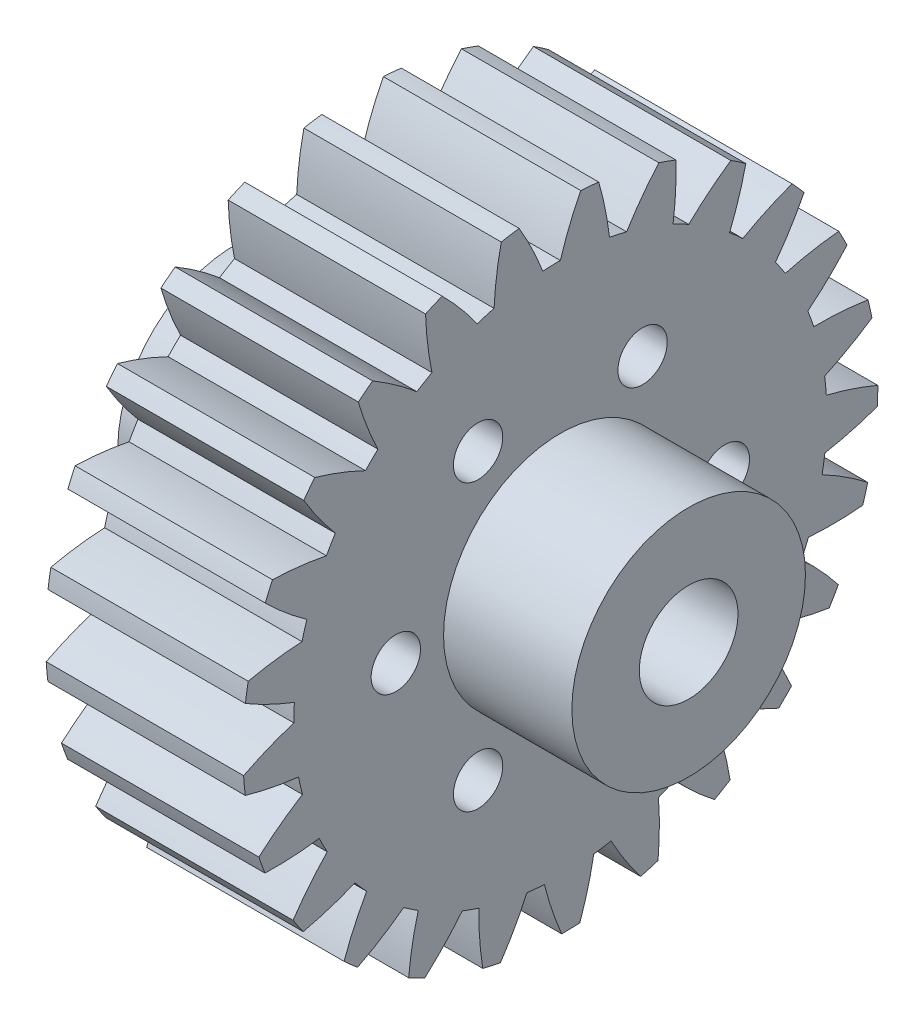
SolidWorks part; units mm, degrees
ref_plane "Front Plane" through (0, 0, 0) normal (0, 0, 1) x (1, 0, 0)
ref_plane "Top Plane" through (0, 0, 0) normal (0, 1, 0) x (1, 0, 0)
ref_plane "Right Plane" through (0, 0, 0) normal (1, 0, 0) x (0, 0, -1)
sketch "Sketch1" plane through (0, 0, 0) normal (1, 0, 0) x (0, 0, -1)
  line L0 (0, 0) -> (1.787, 19.2171) construction
  circle A1 centre (0, 0) radius 19.3 construction
  circle A3 centre (0, 0) radius 3
  arc A5 (1.2387, 19.2602) -> (2.3339, 19.1584) centre (0, 0) cw
  circle A6 centre (0, 0) radius 17.9 construction
  arc A105 (2.7, 17.6952) -> (0.6091, 17.8896) centre (0, 0) ccw
  arc A107 (0, 16.2) -> (1.2387, 19.2602) centre (18.6515, 10.4313) cw
  arc A109 (2.3339, 19.1584) -> (2.9871, 15.9222) centre (-16.4082, 13.6916) cw
  arc A111 (15.4071, 5.0061) -> (15.0442, 6.0095) centre (0, 0) ccw
  arc A113 (7.0251, 17.976) -> (6.853, 14.6791) centre (-12.4878, 17.342) cw
  arc A115 (5.9896, 18.3471) -> (7.0251, 17.976) centre (0, 0) cw
  arc A117 (4.0288, 15.691) -> (5.9896, 18.3471) centre (20.6596, 5.4651) cw
  arc A118 (11.2749, 15.6642) -> (10.2882, 12.5137) centre (-7.7827, 19.9027) cw
  arc A120 (10.3641, 16.2811) -> (11.2749, 15.6642) centre (0, 0) cw
  arc A122 (7.8044, 14.1962) -> (10.3641, 16.2811) centre (21.3697, 0.1556) cw
  arc A124 (14.8162, 12.3681) -> (13.077, 9.562) centre (-2.5886, 21.2129) cw
  arc A126 (14.0875, 13.1922) -> (14.8162, 12.3681) centre (0, 0) cw
  arc A128 (11.0897, 11.8093) -> (14.0875, 13.1922) centre (20.737, -5.1637) cw
  arc A131 (17.4265, 8.2949) -> (15.0442, 6.0095) centre (2.7682, 21.1902) cw
  arc A132 (16.9256, 9.2743) -> (17.4265, 8.2949) centre (0, 0) cw
  arc A134 (13.6781, 8.6804) -> (16.9256, 9.2743) centre (18.8014, -10.1586) cw
  arc A136 (18.9419, 3.7005) -> (16.066, 2.0793) centre (7.951, 19.8361) cw
  arc A138 (18.7003, 4.7737) -> (18.9419, 3.7005) centre (0, 0) cw
  arc A140 (15.4071, 5.0061) -> (18.7003, 4.7737) centre (15.6844, -14.5151) cw
  arc A143 (19.2671, -1.1264) -> (16.0784, -1.9815) centre (12.6343, 17.2355) cw
  arc A145 (19.3, -0.0269) -> (19.2671, -1.1264) centre (0, 0) cw
  arc A146 (16.168, 1.0172) -> (19.3, -0.0269) centre (11.5818, -17.9597) cw
  arc A148 (18.3817, -5.8825) -> (15.0805, -5.9177) centre (16.5236, 13.5521) cw
  arc A150 (18.687, -4.8257) -> (18.3817, -5.8825) centre (0, 0) cw
  arc A153 (15.9131, -3.0356) -> (18.687, -4.8257) centre (6.7516, -20.2757) cw
  arc A154 (16.3413, -10.2691) -> (13.135, -9.4822) centre (19.3748, 9.017) cw
  arc A155 (16.8998, -9.3214) -> (16.3413, -10.2691) centre (0, 0) cw
  arc A156 (14.6582, -6.8976) -> (16.8998, -9.3214) centre (1.4971, -21.3178) cw
  arc A157 (13.2741, -14.0103) -> (10.3642, -12.4508) centre (21.0085, 3.9154) cw
  arc A158 (14.0507, -13.2313) -> (13.2741, -14.0103) centre (0, 0) cw
  arc A159 (12.4823, -10.3263) -> (14.0507, -13.2313) centre (-3.8514, -21.0203) cw
  arc A160 (9.3728, -16.8713) -> (6.9422, -14.6371) centre (21.3222, -1.4322) cw
  arc A161 (10.3188, -16.3099) -> (9.3728, -16.8713) centre (0, 0) cw
  arc A162 (9.5221, -13.1061) -> (10.3188, -16.3099) centre (-8.958, -19.4021) cw
  arc A163 (4.8826, -18.6722) -> (3.084, -15.9037) centre (20.2962, -6.6898) cw
  arc A164 (5.9385, -18.3637) -> (4.8826, -18.6722) centre (0, 0) cw
  arc A165 (5.9636, -15.0624) -> (5.9385, -18.3637) centre (-13.5017, -16.5648) cw
  arc A166 (0.0856, -19.2998) -> (-0.968, -16.1711) centre (17.9949, -11.5271) cw
  arc A167 (1.185, -19.2636) -> (0.0856, -19.2998) centre (0, 0) cw
  arc A168 (2.0304, -16.0723) -> (1.185, -19.2636) centre (-17.197, -12.6867) cw
  arc A169 (-4.7167, -18.7148) -> (-4.9591, -15.4223) centre (14.5628, -15.6401) cw
  arc A170 (-3.6429, -18.9531) -> (-4.7167, -18.7148) centre (0, 0) cw
  arc A171 (-2.0304, -16.0723) -> (-3.6429, -18.9531) centre (-19.8118, -8.0114) cw
  arc A172 (-9.2227, -16.9538) -> (-8.6387, -13.7045) centre (10.2158, -18.7704) cw
  arc A173 (-8.2418, -17.4517) -> (-9.2227, -16.9538) centre (0, 0) cw
  arc A174 (-5.9636, -15.0624) -> (-8.2418, -17.4517) centre (-21.1817, -2.8327) cw
  arc A175 (-13.1492, -14.1276) -> (-11.7755, -11.1256) centre (5.2268, -20.7212) cw
  arc A176 (-12.323, -14.8538) -> (-13.1492, -14.1276) centre (0, 0) cw
  arc A177 (-9.5221, -13.1061) -> (-12.323, -14.8538) centre (-21.2207, 2.524) cw
  arc A178 (-16.2495, -10.4137) -> (-14.1723, -7.8476) centre (-0.0905, -21.3701) cw
  arc A179 (-15.6298, -11.3225) -> (-16.2495, -10.4137) centre (0, 0) cw
  arc A180 (-12.4823, -10.3263) -> (-15.6298, -11.3225) centre (-19.9263, 7.722) cw
  arc A181 (-18.3287, -6.0454) -> (-15.6787, -4.0765) centre (-5.4022, -20.6762) cw
  arc A182 (-17.9546, -7.0798) -> (-18.3287, -6.0454) centre (0, 0) cw
  arc A183 (-14.6582, -6.8976) -> (-17.9546, -7.0798) centre (-17.3799, 12.4349) cw
  arc A184 (-19.2563, -1.2973) -> (-16.1999, -0.0493) centre (-10.3744, -18.6831) cw
  arc A185 (-19.1512, -2.3923) -> (-19.2563, -1.2973) centre (0, 0) cw
  arc A186 (-15.9131, -3.0356) -> (-19.1512, -2.3923) centre (-13.7415, 16.3665) cw
  arc A187 (-18.974, 3.5323) -> (-15.7032, 3.981) centre (-14.6948, -15.5161) cw
  arc A188 (-19.1444, 2.4456) -> (-18.974, 3.5323) centre (0, 0) cw
  arc A189 (-16.168, 1.0172) -> (-19.1444, 2.4456) centre (-9.2396, 19.2696) cw
  arc A190 (-17.4995, 8.14) -> (-14.2199, 7.7611) centre (-18.0919, -11.3742) cw
  arc A191 (-17.9348, 7.1298) -> (-17.4995, 8.14) centre (0, 0) cw
  arc A192 (-15.4071, 5.0061) -> (-17.9348, 7.1298) centre (-4.1571, 20.962) cw
  arc A193 (-14.9253, 12.2362) -> (-11.843, 11.0537) centre (-20.3521, -6.5176) cw
  arc A194 (-15.5982, 11.366) -> (-14.9253, 12.2362) centre (0, 0) cw
  arc A195 (-13.6781, 8.6804) -> (-15.5982, 11.366) centre (1.1865, 21.3373) cw
  arc A196 (-11.4134, 15.5635) -> (-8.722, 13.6516) centre (-21.3336, -1.2515) cw
  arc A197 (-12.2816, 14.888) -> (-11.4134, 15.5635) centre (0, 0) cw
  arc A198 (-11.0897, 11.8093) -> (-12.2816, 14.888) centre (6.4556, 20.3719) cw
  arc A199 (-7.1844, 17.913) -> (-5.053, 15.3918) centre (-20.9746, 4.0933) cw
  arc A200 (-8.1932, 17.4746) -> (-7.1844, 17.913) centre (0, 0) cw
  arc A201 (-7.8044, 14.1962) -> (-8.1932, 17.4746) centre (11.3191, 18.1264) cw
  arc A202 (-2.5039, 19.1369) -> (-1.0664, 16.1649) centre (-19.2977, 9.1809) cw
  arc A203 (-3.5901, 18.9632) -> (-2.5039, 19.1369) centre (0, 0) cw
  arc A204 (-4.0288, 15.691) -> (-3.5901, 18.9632) centre (15.4713, 14.742) cw
  arc A205 (13.6781, 8.6804) -> (13.077, 9.562) centre (0, 0) ccw
  arc A206 (11.0897, 11.8093) -> (10.2882, 12.5137) centre (0, 0) ccw
  arc A207 (7.8044, 14.1962) -> (6.853, 14.6791) centre (0, 0) ccw
  arc A208 (4.0288, 15.691) -> (2.9871, 15.9222) centre (0, 0) ccw
  arc A209 (16.168, 1.0172) -> (16.066, 2.0793) centre (0, 0) ccw
  arc A210 (15.9131, -3.0356) -> (16.0784, -1.9815) centre (0, 0) ccw
  arc A211 (14.6582, -6.8976) -> (15.0805, -5.9177) centre (0, 0) ccw
  arc A212 (12.4823, -10.3263) -> (13.135, -9.4822) centre (0, 0) ccw
  arc A213 (9.5221, -13.1061) -> (10.3642, -12.4508) centre (0, 0) ccw
  arc A214 (5.9636, -15.0624) -> (6.9422, -14.6371) centre (0, 0) ccw
  arc A215 (2.0304, -16.0723) -> (3.084, -15.9037) centre (0, 0) ccw
  arc A216 (-2.0304, -16.0723) -> (-0.968, -16.1711) centre (0, 0) ccw
  arc A217 (-5.9636, -15.0624) -> (-4.9591, -15.4223) centre (0, 0) ccw
  arc A218 (-9.5221, -13.1061) -> (-8.6387, -13.7045) centre (0, 0) ccw
  arc A219 (-12.4823, -10.3263) -> (-11.7755, -11.1256) centre (0, 0) ccw
  arc A220 (-14.6582, -6.8976) -> (-14.1723, -7.8476) centre (0, 0) ccw
  arc A221 (-15.9131, -3.0356) -> (-15.6787, -4.0765) centre (0, 0) ccw
  arc A222 (-16.168, 1.0172) -> (-16.1999, -0.0493) centre (0, 0) ccw
  arc A223 (-15.4071, 5.0061) -> (-15.7032, 3.981) centre (0, 0) ccw
  arc A224 (-13.6781, 8.6804) -> (-14.2199, 7.7611) centre (0, 0) ccw
  arc A225 (-4.0288, 15.691) -> (-5.053, 15.3918) centre (0, 0) ccw
  arc A226 (-7.8044, 14.1962) -> (-8.722, 13.6516) centre (0, 0) ccw
  arc A227 (-11.0897, 11.8093) -> (-11.843, 11.0537) centre (0, 0) ccw
  arc A228 (0, 16.2) -> (-1.0664, 16.1649) centre (0, 0) ccw
  circle A229 centre (0, 0) radius 10 construction
  circle A230 centre (10, 0) radius 1.5
  circle A231 centre (5, -8.6603) radius 1.5
  circle A232 centre (-5, -8.6603) radius 1.5
  circle A233 centre (-10, 0) radius 1.5
  circle A234 centre (-5, 8.6603) radius 1.5
  circle A235 centre (5, 8.6603) radius 1.5
  point P10 (1.787, 19.2171)
  point P13 (1.6574, 17.8231)
  point P160 (0, 0)
  point P165 (0, 0)
  point P177 (0, 0)
  dimension "D1" = 32.4
  dimension "D2" = 38.6
  dimension "D3" = 6
  dimension "D4" = 3
  dimension "D6" = 2.1
  dimension "D7" = 35.8
  dimension "D5" = 1.1
extrude "Boss-Extrude1" add sketch "Sketch1" along normal blind 12 contours A107 A228 A202 A203 A204 A225 A199 A200 A201 A226 A196 A197 A198 A227 A193 A194 A195 A224 A190 A191 A192 A223 A187 A188 A189 A222 A184 A185 A186 A221 A181 A182 A183 A220 A178 A179 A180 A219 A175 A176 A177 A218 A172 A173 A174 A217 A169 A170 A171 A216 A166 | A109 A5 A107 A105
sketch "Sketch2" plane through (12, 0, 0) normal (1, 0, 0) x (0, 0, -1)
  circle A0 centre (0, 0) radius 7.1
  circle A1 centre (0, 0) radius 3
  dimension "D1" = 6
  dimension "D2" = 14.2
extrude "Boss-Extrude2" add sketch "Sketch2" along normal blind 7.8 and the other way blind 19.8
